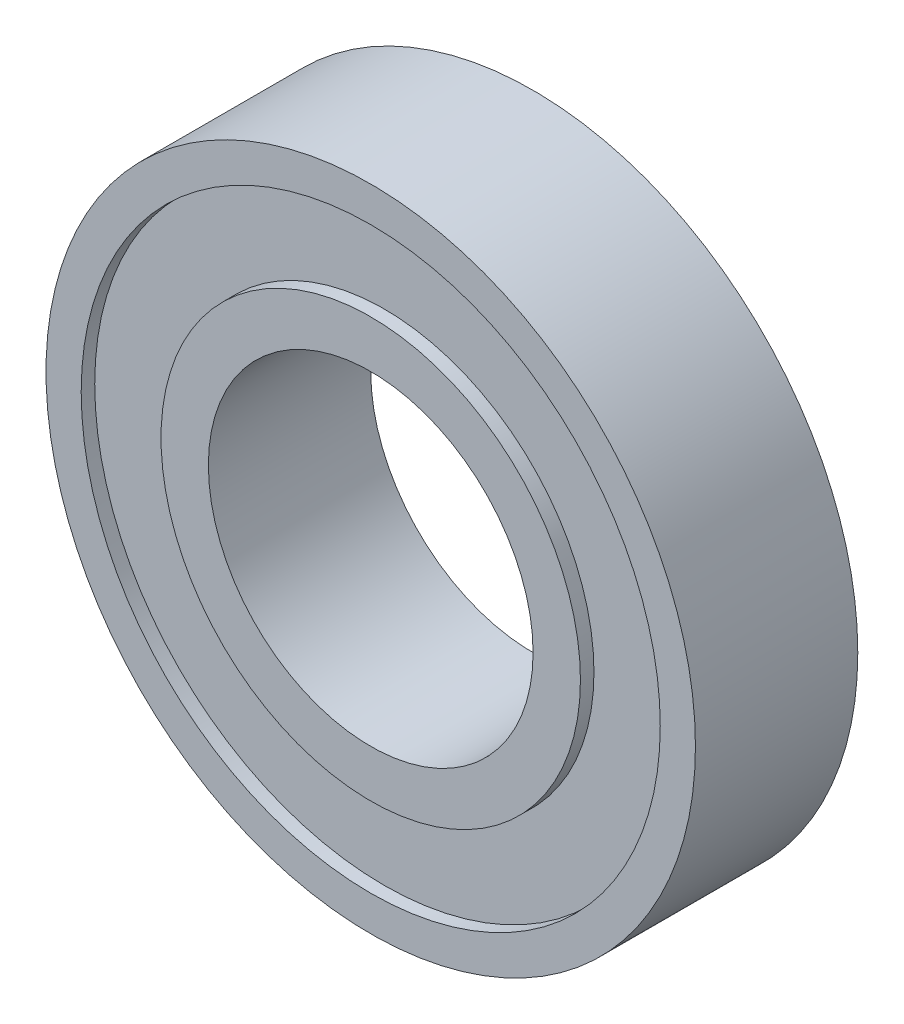
SolidWorks part; units mm, degrees
material "201 退火不鏽鋼 (SS)"
ref_plane "前基準面" through (0, 0, 0) normal (0, 0, 1) x (1, 0, 0)
ref_plane "上基準面" through (0, 0, 0) normal (0, 1, 0) x (1, 0, 0)
ref_plane "右基準面" through (0, 0, 0) normal (1, 0, 0) x (0, 0, -1)
sketch "草圖1" plane through (0, 0, 0) normal (0, 0, 1) x (1, 0, 0)
  circle A0 centre (0, 0) radius 12
  dimension "D1" = 24
extrude "填料-伸長1" add sketch "草圖1" along normal mid plane 6
sketch "草圖2" plane through (0, 0, 3) normal (0, 0, 1) x (1, 0, 0)
  circle A0 centre (0, 0) radius 6
  dimension "D1" = 12
extrude "除料-伸長1" cut sketch "草圖2" against normal through all
sketch "草圖3" plane through (0, 0, 3) normal (0, 0, 1) x (1, 0, 0)
  circle A0 centre (0, 0) radius 7.75
  circle A1 centre (0, 0) radius 10.7
  dimension "D1" = 21.4
  dimension "D2" = 15.5
extrude "除料-伸長2" cut sketch "草圖3" against normal blind 0.5
mirror "鏡射1" about plane through (0, 0, 0) normal (0, 0, 1) of "除料-伸長2"
